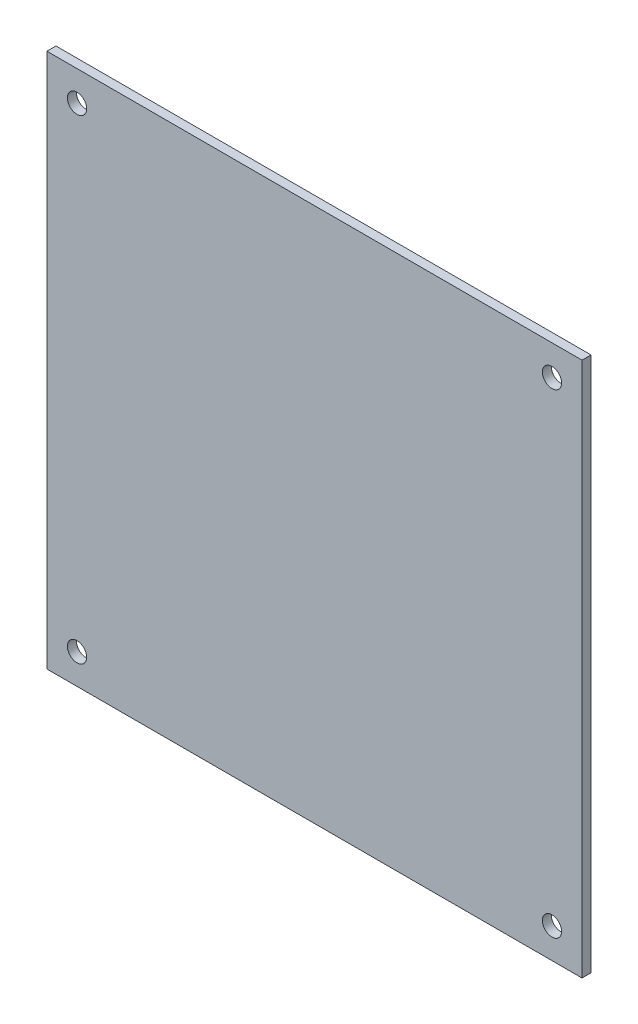
SolidWorks part; units mm, degrees
ref_plane "Front Plane" through (0, 0, 0) normal (0, 0, 1) x (1, 0, 0)
ref_plane "Top Plane" through (0, 0, 0) normal (0, 1, 0) x (1, 0, 0)
ref_plane "Right Plane" through (0, 0, 0) normal (1, 0, 0) x (0, 0, -1)
sketch "Esquisse1" plane through (0, 0, 0) normal (0, 0, 1) x (1, 0, 0)
  line L1 (-44.5, 44.5) -> (44.5, 44.5)
  line L2 (-44.5, 44.5) -> (-44.5, -44.5)
  line L3 (-44.5, -44.5) -> (44.5, -44.5)
  line L4 (44.5, 44.5) -> (44.5, -44.5)
  circle A0 centre (-39.5, 39.5) radius 1.6
  circle A1 centre (-39.5, -39.5) radius 1.6
  circle A2 centre (39.5, -39.5) radius 1.6
  circle A3 centre (39.5, 39.5) radius 1.6
  point P4 (-44.5, 0)
  point P5 (0, -44.5)
  dimension "D3" = 3.2
  dimension "D1" = 89
  dimension "D2" = 89
  dimension "D4" = 5
  dimension "D5" = 5
  dimension "D6" = 5
  dimension "D7" = 5
extrude "Main" add sketch "Esquisse1" along normal blind 1.5
